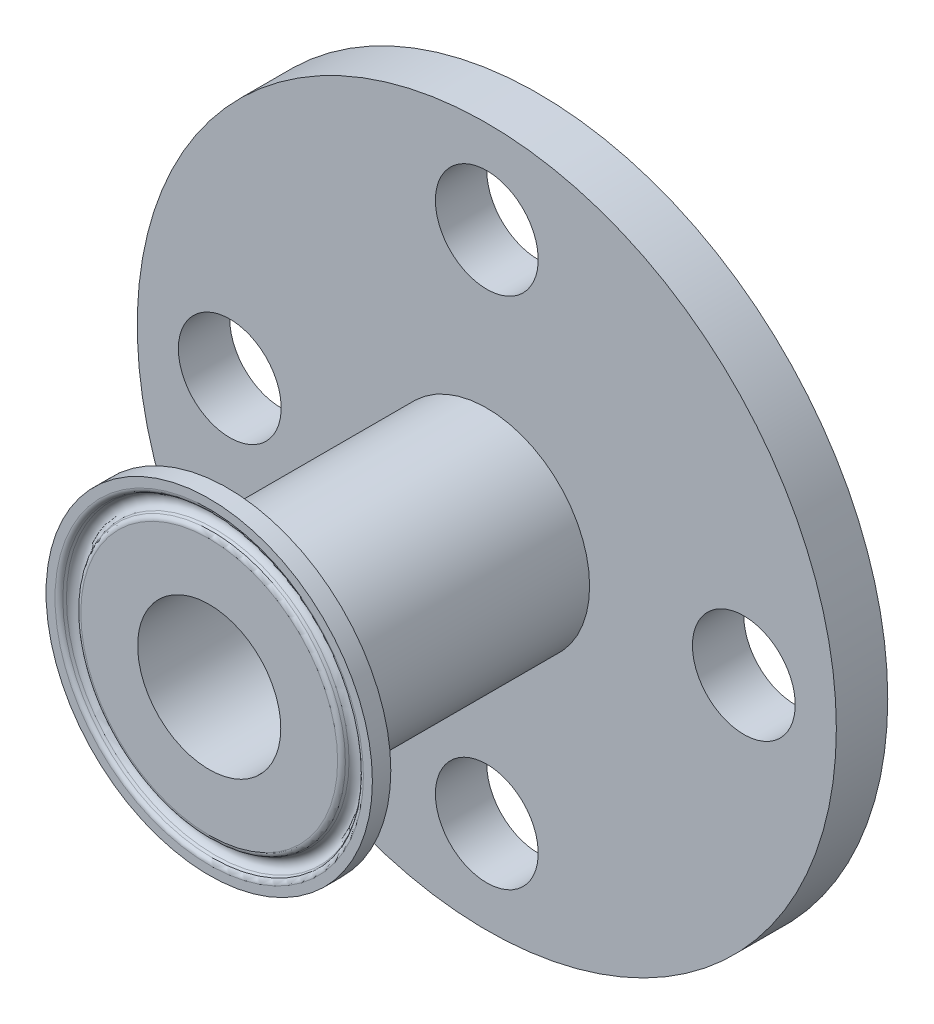
SolidWorks part; units mm, degrees
ref_plane "Front Plane" through (0, 0, 0) normal (0, 0, 1) x (1, 0, 0)
ref_plane "Top Plane" through (0, 0, 0) normal (0, 1, 0) x (1, 0, 0)
ref_plane "Right Plane" through (0, 0, 0) normal (1, 0, 0) x (0, 0, -1)
sketch "Sketch1" plane through (0, 0, 0) normal (1, 0, 0) x (0, 0, -1)
  line L0 (0, 0) -> (50.8, 0) construction
  line L1 (0, 11.049) -> (0, 19.828)
  line L2 (0, 25.1968) -> (2.8448, 25.1968)
  line L3 (2.8448, 25.1968) -> (5.4773, 17.9641)
  line L4 (8.4608, 15.875) -> (42.8625, 15.875)
  line L5 (0, 23.8092) -> (0, 25.1968)
  line L6 (0.4797, 23.0844) -> (0.8729, 22.9175)
  line L7 (0.4797, 20.5528) -> (0.8729, 20.7197)
  line L8 (0, 23.288) -> (0, 20.3492) construction
  line L9 (0, 21.8186) -> (0.4064, 21.8186) construction
  line L10 (0, 11.049) -> (0, 0) construction
  line L11 (50.8, 28.575) -> (50.8, 11.049)
  line L12 (50.8, 11.049) -> (0, 11.049)
  line L13 (42.8625, 15.875) -> (42.8625, 53.975)
  line L14 (42.8625, 53.975) -> (50.8, 53.975)
  line L16 (50.8, 28.575) -> (50.8, 53.975)
  line L17 (42.8625, 39.6875) -> (50.8, 39.6875) construction
  line L18 (46.8313, 39.6875) -> (46.8313, 47.625) construction
  line L19 (46.8313, 39.6875) -> (46.8313, 31.75) construction
  arc A0 (0.8729, 20.7197) -> (0.8729, 22.9175) centre (0.4064, 21.8186) ccw
  arc A2 (0, 19.828) -> (0.4797, 20.5528) centre (0.7874, 19.828) cw
  arc A3 (0, 23.8092) -> (0.4797, 23.0844) centre (0.7874, 23.8092) ccw
  arc A4 (5.4773, 17.9641) -> (8.4608, 15.875) centre (8.4608, 19.05) ccw
  point P31 (0, 0)
  point P33 (0, 0)
  point P34 (0, 0)
  dimension "D5" = 1.1938
  dimension "D4" = 0.7874
  dimension "R" = 3.175
  dimension "D1" = 20
  dimension "D2" = 23
  dimension "D3" = 46
  dimension "F" = 2.8448
  dimension "D6" = 0.4064
  dimension "SealDia" = 43.6372
  dimension "FlangeOD" = 50.3936
  dimension "ShaftDia" = 31.75
  dimension "MinID" = 22.098
  dimension "Length" = 50.8
  dimension "BoltFlangeOD" = 107.95
  dimension "BoltCircleDia" = 79.375
  dimension "HoleDia" = 15.875
  dimension "D10" = 7.9375
revolve "Revolve1" add sketch "Sketch1" angle 360 about L0
sketch "Sketch2" plane through (0, 0, -50.8) normal (0, 0, -1) x (-1, 0, 0)
  circle A0 centre (0, 0) radius 39.6875 construction
  circle A1 centre (0, 39.6875) radius 7.9375
  circle A2 centre (39.6875, 0) radius 7.9375
  circle A3 centre (0, -39.6875) radius 7.9375
  circle A4 centre (-39.6875, 0) radius 7.9375
  point P16 (0, 0)
  dimension "D1" = 4
extrude "Cut-Extrude1" cut sketch "Sketch2" against normal up to surface (7.9375 mm away) up to face at (15.875, 0, -42.8625)
